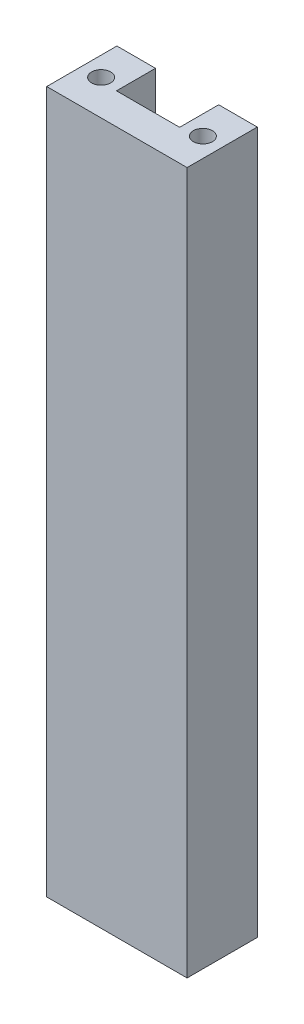
SolidWorks part; units mm, degrees
ref_plane "Front Plane" through (0, 0, 0) normal (0, 0, 1) x (1, 0, 0)
ref_plane "Top Plane" through (0, 0, 0) normal (0, 1, 0) x (1, 0, 0)
ref_plane "Right Plane" through (0, 0, 0) normal (1, 0, 0) x (0, 0, -1)
sketch "Sketch1" plane through (0, 0, 0) normal (0, 1, 0) x (1, 0, 0)
  line L0 (6.985, 0) -> (6.985, -7.0652)
  line L2 (0, 0) -> (0, -12.7)
  line L3 (0, -12.7) -> (25.4, -12.7)
  line L4 (25.4, 0) -> (25.4, -12.7)
  line L5 (6.985, -7.0652) -> (18.415, -7.0652)
  line L6 (18.415, -7.0652) -> (18.415, 0)
  line L7 (18.415, 0) -> (6.985, 0)
  line L8 (0, 0) -> (6.985, 0)
  line L9 (18.415, 0) -> (25.4, 0)
  dimension "D1" = 12.7
  dimension "D2" = 25.4
  dimension "D3" = 11.43
extrude "Boss-Extrude1" add sketch "Sketch1" along normal blind 127 contours L9 L6 L5 L0 L8 L2 L3 L4
sketch "Sketch2" plane through (0, 0, 0) normal (0, -1, 0) x (1, 0, 0)
  line L0 (0, 6.35) -> (25.4, 6.35) construction
  line L1 (0, 12.7) -> (25.4, 12.7)
  line L2 (0, 12.7) -> (0, 0)
  line L3 (0, 0) -> (25.4, 0)
  line L4 (25.4, 12.7) -> (25.4, 0)
  line L5 (6.985, 0) -> (0, 0)
  line L6 (3.4925, 0) -> (3.4925, 6.35) construction
  line L7 (25.4, 0) -> (18.415, 0)
  line L8 (21.9075, 0) -> (21.9075, 6.35) construction
hole_wizard "Tap Drill for #8-32 Tap2" positions "3DSketch1" profile "Sketch3" hole size "#8-32" standard "ANSI Inch"
sketch3d "3DSketch1"
  point P0 (3.4925, 0, 6.35)
  point P3 (21.9075, 0, 6.35)
sketch "Sketch3" plane through (3.4925, 0, 6.35) normal (1, 0, 0) x (0, 0, -1)
  line L0 (0, 0) -> (0, 15.0078)
  line L1 (0, 15.0078) -> (1.7272, 13.97)
  line L2 (1.7272, 13.97) -> (1.7272, 0)
  line L5 (1.7272, 0) -> (0, 0)
  line L10 (0, 15.0078) -> (-1.7272, 13.97) construction
  line L11 (0, -6.35) -> (0, 107.95) construction
  dimension "Hole Dia." = 3.4544
  dimension "Hole Depth" = 13.97
  dimension "Drill Angle" = 118
sketch "Sketch4" plane through (0, 127, 0) normal (0, 1, 0) x (1, 0, 0)
  point P0 (3.4925, -6.35)
  point P1 (21.9075, -6.35)
hole_wizard "Tap Drill for #8-32 Tap3" positions "3DSketch2" profile "Sketch5" hole size "#8-32" standard "ANSI Inch"
sketch3d "3DSketch2"
  point P0 (3.4925, 127, 6.35)
  point P3 (21.9075, 127, 6.35)
sketch "Sketch5" plane through (3.4925, 127, 6.35) normal (1, 0, 0) x (0, 0, 1)
  line L0 (0, 0) -> (0, 15.0078)
  line L1 (0, 15.0078) -> (1.7272, 13.97)
  line L2 (1.7272, 13.97) -> (1.7272, 0)
  line L5 (1.7272, 0) -> (0, 0)
  line L10 (0, 15.0078) -> (-1.7272, 13.97) construction
  line L11 (0, -6.35) -> (0, 107.95) construction
  dimension "Hole Dia." = 3.4544
  dimension "Hole Depth" = 13.97
  dimension "Drill Angle" = 118
